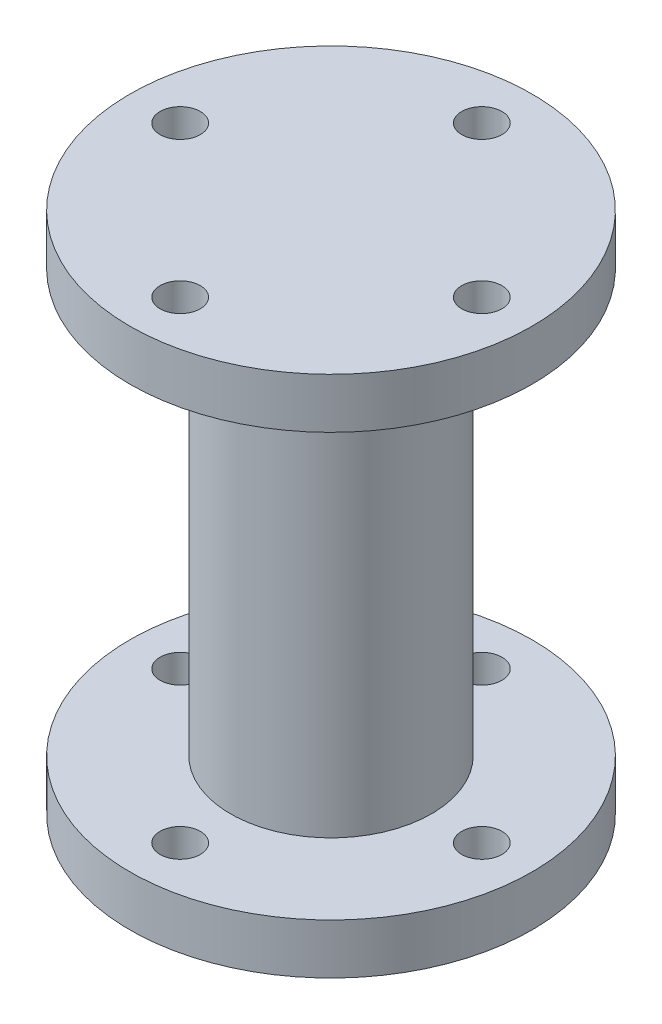
SolidWorks part; units mm, degrees
material "ABS"
ref_plane "Front Plane" through (0, 0, 0) normal (0, 0, 1) x (1, 0, 0)
ref_plane "Top Plane" through (0, 0, 0) normal (0, 1, 0) x (1, 0, 0)
ref_plane "Right Plane" through (0, 0, 0) normal (1, 0, 0) x (0, 0, -1)
sketch "Sketch1" plane through (0, 0, 0) normal (0, 1, 0) x (1, 0, 0)
  circle A0 centre (0, 0) radius 20
  circle A1 centre (0, 0) radius 15 construction
  circle A2 centre (0, 15) radius 2
  circle A3 centre (15, 0) radius 2
  circle A4 centre (0, -15) radius 2
  circle A5 centre (-15, 0) radius 2
  point P15 (0, 0)
  dimension "D1" = 4
  dimension "D2" = 4
  dimension "D5" = 30
  dimension "D6" = 40
extrude "Boss-Extrude1" add sketch "Sketch1" along normal blind 5
sketch "Sketch2" plane through (0, 0, 0) normal (0, -1, 0) x (1, 0, 0)
  circle A0 centre (0, 0) radius 10
  circle A1 centre (0, 0) radius 20 construction
  dimension "D1" = 20
extrude "Boss-Extrude2" add sketch "Sketch2" along normal blind 42
sketch "Sketch3" plane through (0, -42, 0) normal (0, -1, 0) x (1, 0, 0)
  circle A0 centre (-15, 0) radius 2 construction
  circle A1 centre (0, 0) radius 10
  circle A2 centre (0, 0) radius 10
  circle A3 centre (0, 0) radius 20
  circle A4 centre (0, 0) radius 20
  circle A5 centre (0, -15) radius 2 construction
  circle A6 centre (15, 0) radius 2 construction
  circle A7 centre (0, 15) radius 2 construction
  circle A8 centre (-15, 0) radius 2
  circle A9 centre (0, -15) radius 2
  circle A10 centre (15, 0) radius 2
  circle A11 centre (0, 15) radius 2
  dimension "D1" = 0
  dimension "D2" = 0
extrude "Boss-Extrude3" add sketch "Sketch3" along normal blind 5 separate body
